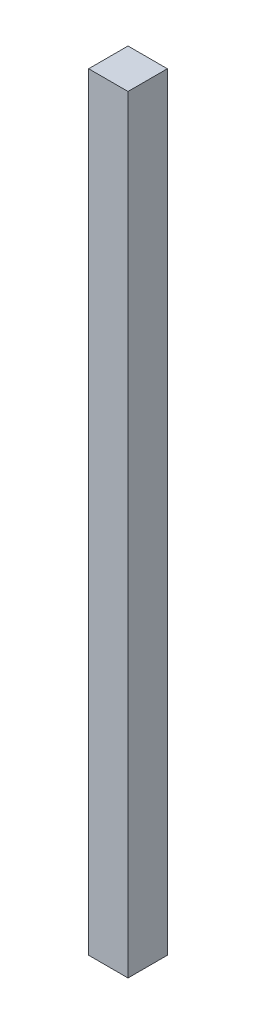
SolidWorks part; units mm, degrees
ref_plane "Front Plane" through (0, 0, 0) normal (0, 0, 1) x (1, 0, 0)
ref_plane "Top Plane" through (0, 0, 0) normal (0, 1, 0) x (1, 0, 0)
ref_plane "Right Plane" through (0, 0, 0) normal (1, 0, 0) x (0, 0, -1)
sketch "Sketch2" plane through (0, 0, 0) normal (0, 0, 1) x (1, 0, 0)
  line L1 (-1.5875, -30.9601) -> (1.5875, -30.9601)
  line L2 (-1.5875, -30.9601) -> (-1.5875, 30.9601)
  line L3 (-1.5875, 30.9601) -> (1.5875, 30.9601)
  line L4 (1.5875, -30.9601) -> (1.5875, 30.9601)
  line L5 (-1.5875, -30.9601) -> (1.5875, 30.9601) construction
  line L6 (-1.5875, 30.9601) -> (1.5875, -30.9601) construction
  point P0 (0, 0)
  dimension "D1" = 3.175
  dimension "D2" = 61.9201
extrude "Boss-Extrude1" add sketch "Sketch2" along normal blind 3.175
equation "\"side thickness\"= 1 / 8in"
equation "\"extrude thickness\"= 1 / 8in"
equation "\"length\"= 2.3898 + 0.048in"
equation "\"D1@Sketch2\"=\"side thickness\""
equation "\"D2@Sketch2\"=\"length\""
equation "\"D1@Boss-Extrude1\"=\"extrude thickness\""
